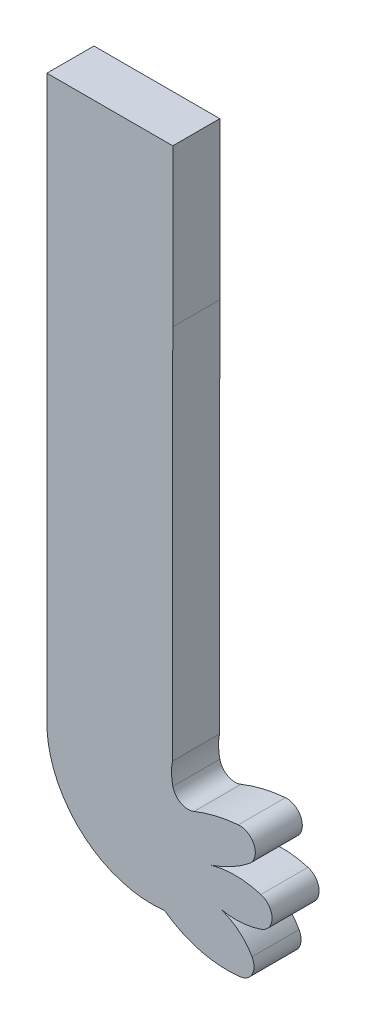
SolidWorks part; units mm, degrees
ref_plane "Alzado" through (0, 0, 0) normal (0, 0, 1) x (1, 0, 0)
ref_plane "Planta" through (0, 0, 0) normal (0, 1, 0) x (1, 0, 0)
ref_plane "Vista lateral" through (0, 0, 0) normal (1, 0, 0) x (0, 0, -1)
sketch "Model" plane through (0, 0, 0) normal (0, 0, 1) x (1, 0, 0)
  line L0 (57.8761, 16.1935) -> (57.894, 40.1803)
  line L1 (57.894, 40.1803) -> (57.894, 50.1803)
  line L2 (57.894, 50.1803) -> (49.8679, 50.1803)
  line L3 (49.8679, 50.1803) -> (49.8679, 31.5971)
  line L4 (49.8679, 31.5971) -> (49.8679, 14.0138)
  arc A0 (60.8974, 9.5627) -> (63.5166, 9.7231) centre (61.9279, 14.2004) ccw
  arc A1 (63.5166, 9.7231) -> (63.5166, 11.6376) centre (63.2274, 10.6803) ccw
  arc A2 (63.5166, 11.6376) -> (60.3679, 11.6803) centre (61.8679, 6.1803) ccw
  arc A3 (60.3679, 11.6803) -> (62.779, 12.9851) centre (57.8679, 19.1803) ccw
  arc A4 (62.779, 12.9851) -> (62.0754, 14.7653) centre (62.1578, 13.7687) ccw
  arc A5 (62.0754, 14.7653) -> (59.2493, 14.0913) centre (62.8679, 5.1803) ccw
  arc A6 (57.8972, 14.7996) -> (59.2493, 14.0913) centre (58.8731, 15.0179) ccw
  arc A7 (57.8761, 16.1935) -> (57.8972, 14.7996) centre (61.2414, 15.5475) ccw
  arc A8 (49.8679, 14.0138) -> (57.3679, 7.6803) centre (56.5485, 14.3174) ccw
  arc A9 (57.3679, 7.6803) -> (62.2004, 6.4308) centre (61.3679, 13.1803) ccw
  arc A10 (62.2004, 6.4308) -> (62.9496, 7.9134) centre (62.078, 7.4232) ccw
  arc A11 (62.9496, 7.9134) -> (60.8974, 9.5627) centre (59.8679, 6.1803) ccw
extrude "Saliente-Extruir1" add sketch "Model" along normal blind 3
